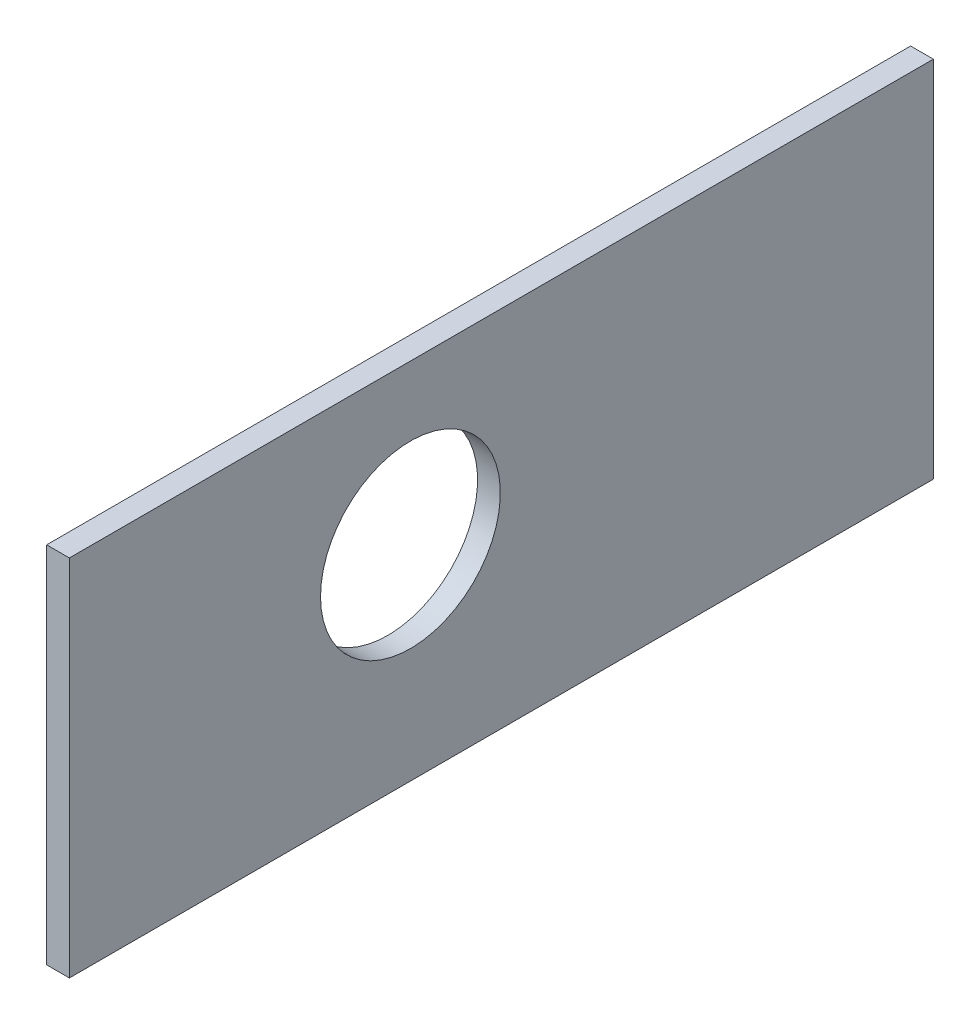
SolidWorks part; units mm, degrees
material "6061-T6 (SS)"
ref_plane "Front Plane" through (0, 0, 0) normal (0, 0, 1) x (1, 0, 0)
ref_plane "Top Plane" through (0, 0, 0) normal (0, 1, 0) x (1, 0, 0)
ref_plane "Right Plane" through (0, 0, 0) normal (1, 0, 0) x (0, 0, -1)
sketch "Sketch1" plane through (0, 0, 0) normal (0, 1, 0) x (1, 0, 0)
  line L1 (101.6, -60.325) -> (-101.6, -60.325)
  line L2 (101.6, -60.325) -> (101.6, 60.325)
  line L3 (101.6, 60.325) -> (-101.6, 60.325)
  line L4 (-101.6, -60.325) -> (-101.6, 60.325)
  line L5 (101.6, -60.325) -> (-101.6, 60.325) construction
  line L6 (101.6, 60.325) -> (-101.6, -60.325) construction
  point P0 (0, 0)
  dimension "D1" = 120.65
  dimension "D2" = 203.2
extrude "Boss-Extrude1" add sketch "Sketch1" along normal blind 50.8
sketch "Sketch2" plane through (0, 50.8, 0) normal (0, 1, 0) x (1, 0, 0)
  line L8 (-98.425, 57.15) -> (-98.425, -57.15)
  line L9 (98.425, 57.15) -> (-98.425, 57.15)
  line L10 (98.425, -57.15) -> (98.425, 57.15)
  line L11 (-98.425, -57.15) -> (98.425, -57.15)
  line L12 (-98.425, 57.15) -> (-98.425, -57.15)
  line L13 (98.425, 57.15) -> (-98.425, 57.15)
  line L14 (98.425, -57.15) -> (98.425, 57.15)
  line L15 (-98.425, -57.15) -> (98.425, -57.15)
  dimension "D1" = 3.175
extrude "Cut-Extrude1" cut sketch "Sketch2" against normal through all
sketch "Sketch4" plane through (0, 50.8, 0) normal (0, 1, 0) x (1, 0, 0)
  line L4 (101.6, 60.325) -> (-101.6, 60.325)
  line L5 (-101.6, 60.325) -> (-101.6, -60.325)
  line L6 (-101.6, -60.325) -> (101.6, -60.325)
  line L7 (101.6, -60.325) -> (101.6, 60.325)
  line L9 (-98.425, -57.15) -> (98.425, -57.15)
  line L10 (-98.425, -57.15) -> (-98.425, 57.15)
  line L11 (-98.425, 57.15) -> (98.425, 57.15)
  line L12 (98.425, -57.15) -> (98.425, 57.15)
  line L13 (-98.425, -57.15) -> (98.425, 57.15) construction
  line L14 (-98.425, 57.15) -> (98.425, -57.15) construction
  point P12 (0, 0)
  dimension "D1" = 3.175
  dimension "D2" = 3.175
  dimension "D3" = 3.175
  dimension "D4" = 3.175
extrude "Boss-Extrude2" add sketch "Sketch4" against normal blind 6.35
sketch "Sketch10" plane through (0, 0, 60.325) normal (0, 0, 1) x (1, 0, 0)
  line L0 (0, 22.225) -> (50.8, 22.225) construction
  line L1 (-101.6, 0) -> (101.6, 0) construction
  line L3 (-104.775, 13.4874) -> (104.775, 13.4874)
  line L6 (50.8, 22.225) -> (101.6, 22.225) construction
  line L7 (101.6, 50.8) -> (101.6, 0) construction
  line L8 (0, 22.225) -> (-50.8, 22.225) construction
  line L9 (-50.8, 22.225) -> (-101.6, 22.225) construction
  line L10 (-101.6, 50.8) -> (-101.6, 0) construction
  circle A0 centre (-76.2, 22.225) radius 10.2489
  circle A1 centre (-25.4, 22.225) radius 10.2489
  circle A2 centre (25.4, 22.225) radius 10.2489
  circle A3 centre (76.2, 22.225) radius 10.2489
  point P5 (-76.2, 22.225)
  point P9 (-25.4, 22.225)
  point P12 (25.4, 22.225)
  point P13 (76.2, 22.225)
  dimension "D2" = 22.225
  dimension "D1" = 20.4978
  dimension "D3" = 8.7376
extrude "Cut-Extrude5" cut sketch "Sketch10" against normal through all
sketch "Sketch12" plane through (101.6, 0, 0) normal (1, 0, 0) x (0, 0, -1)
  line L0 (60.325, 22.225) -> (-60.325, 22.225) construction
  line L1 (60.325, 50.8) -> (60.325, 0) construction
  line L2 (-60.325, 50.8) -> (-60.325, 0) construction
  line L4 (-60.325, 13.4874) -> (60.325, 13.4874)
  circle A0 centre (-22.225, 22.225) radius 10.2489
  circle A1 centre (22.225, 22.225) radius 10.2489
  point P6 (60.325, 22.225)
  point P7 (-22.225, 22.225)
  point P10 (22.225, 22.225)
  dimension "D2" = 8.7376
  dimension "D3" = 20.4978
  dimension "D1" = 38.1
  dimension "D4" = 38.1
extrude "Cut-Extrude6" cut sketch "Sketch12" against normal up to next
sketch "Sketch13" plane through (-101.6, 0, 0) normal (-1, 0, 0) x (0, 0, 1)
  line L0 (60.325, 25.4) -> (-60.325, 25.4) construction
  line L1 (60.325, 50.8) -> (60.325, 0) construction
  line L2 (-60.325, 50.8) -> (-60.325, 0) construction
  line L4 (-60.325, 50.8) -> (60.325, 50.8) construction
  circle A0 centre (12.7, 28.575) radius 12.554
  point P6 (22.225, 25.4)
  point P7 (12.7, 28.575)
  dimension "D3" = 25.1079
  dimension "D4" = 22.225
  dimension "D1" = 38.1
  dimension "D2" = 73.025
extrude "Cut-Extrude7" cut sketch "Sketch13" against normal up to next
sketch "Sketch14" plane through (0, 50.8, 0) normal (0, 1, 0) x (1, 0, 0)
  line L0 (-98.425, -57.15) -> (-98.425, -60.325)
  line L1 (-101.6, -60.325) -> (101.6, -60.325) construction
  line L2 (-98.425, -60.325) -> (101.6, -60.325)
  line L3 (101.6, -60.325) -> (101.6, 60.325)
  line L4 (101.6, 60.325) -> (-98.425, 60.325)
  line L5 (101.6, 60.325) -> (-101.6, 60.325) construction
  line L6 (-98.425, 60.325) -> (-98.425, -57.15)
extrude "Cut-Extrude8" cut sketch "Sketch14" against normal through all
